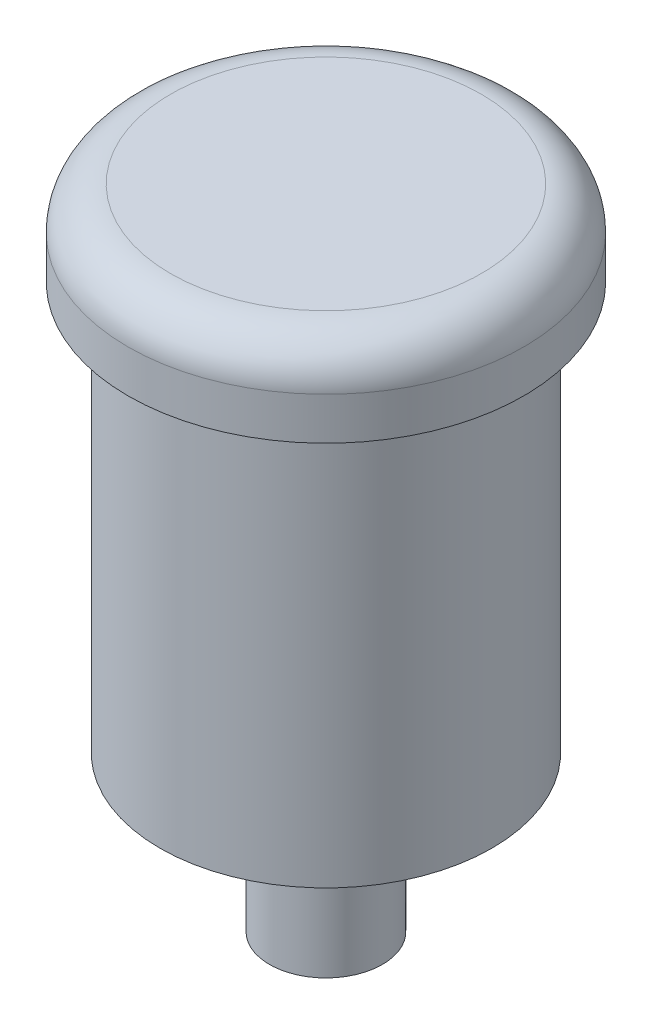
SolidWorks part; units mm, degrees
ref_plane "Front Plane" through (0, 0, 0) normal (0, 0, 1) x (1, 0, 0)
ref_plane "Top Plane" through (0, 0, 0) normal (0, 1, 0) x (1, 0, 0)
ref_plane "Right Plane" through (0, 0, 0) normal (1, 0, 0) x (0, 0, -1)
sketch "Sketch1" plane through (0, 0, 0) normal (0, 1, 0) x (1, 0, 0)
  circle A0 centre (-10.4256, 8.3272) radius 14
  dimension "D1" = 28
extrude "Boss-Extrude1" add sketch "Sketch1" along normal blind 6
sketch "Sketch2" plane through (0, 0, 0) normal (0, -1, 0) x (1, 0, 0)
  circle A0 centre (-10.4256, -8.3272) radius 11.75
  point P0 (-10.4256, -8.3272)
  dimension "D1" = 23.5
extrude "Boss-Extrude2" add sketch "Sketch2" along normal blind 28.85
fillet "Fillet1" radius 3 1 edges at (-10.4256, 6, 5.6728)
sketch "Sketch3" plane through (0, -28.85, 0) normal (0, -1, 0) x (1, 0, 0)
  circle A0 centre (-10.4256, -8.3272) radius 4
  point P0 (-10.4256, -8.3272)
  dimension "D1" = 8
extrude "Boss-Extrude3" add sketch "Sketch3" along normal blind 11
